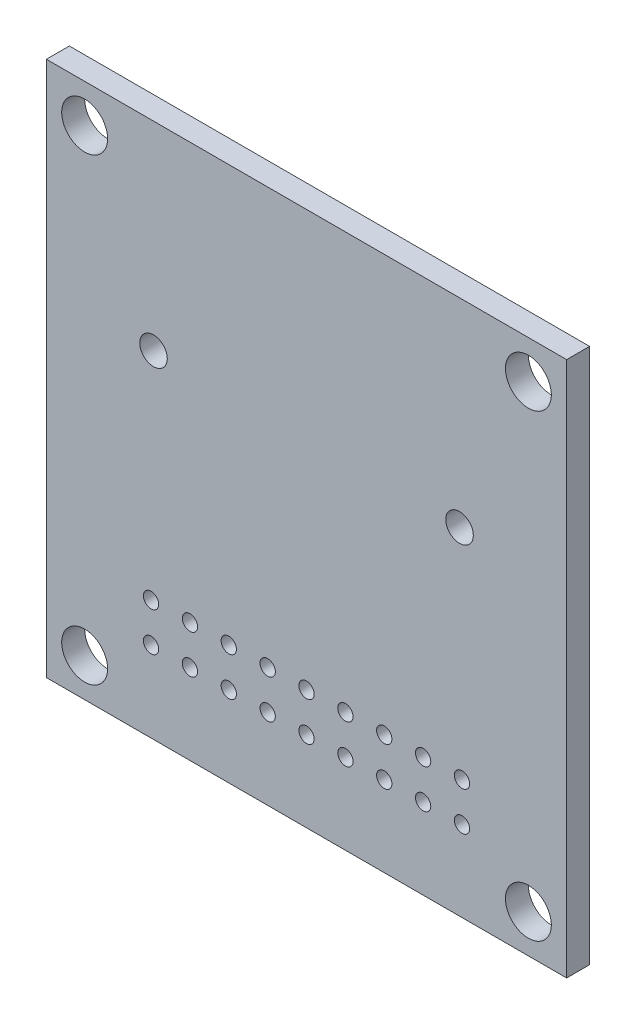
SolidWorks part; units mm, degrees
ref_plane "Front Plane" through (0, 0, 0) normal (0, 0, 1) x (1, 0, 0)
ref_plane "Top Plane" through (0, 0, 0) normal (0, 1, 0) x (1, 0, 0)
ref_plane "Right Plane" through (0, 0, 0) normal (1, 0, 0) x (0, 0, -1)
sketch "Sketch1" plane through (0, 0, 0) normal (0, 0, 1) x (1, 0, 0)
  line L0 (0, 0) -> (0, 8.3377) construction
  line L1 (17, -17.5) -> (-17, -17.5)
  line L2 (17, -17.5) -> (17, 17.5)
  line L3 (17, 17.5) -> (-17, 17.5)
  line L4 (-17, -17.5) -> (-17, 17.5)
  line L5 (17, -17.5) -> (-17, 17.5) construction
  line L6 (17, 17.5) -> (-17, -17.5) construction
  line L7 (0, 0) -> (4.1078, 0) construction
  circle A0 centre (-14.5, 15) radius 1.5
  circle A1 centre (-14.5, -15) radius 1.5
  circle A2 centre (14.5, -15) radius 1.5
  circle A3 centre (14.5, 15) radius 1.5
  point P0 (0, 0)
  dimension "D3" = 3
  dimension "D4" = 29
  dimension "D1" = 34
  dimension "D2" = 35
  dimension "D5" = 30
extrude "Board" add sketch "Sketch1" along normal blind 1.5
sketch "Sketch2" plane through (0, 0, 0) normal (0, 0, -1) x (-1, 0, 0)
  line L0 (17, -17.5) -> (-17, -17.5) construction
  circle A0 centre (-10, 4.5) radius 0.9
  circle A1 centre (10, 4.5) radius 0.9
  circle A2 centre (10.16, -9.69) radius 0.5
  circle A3 centre (10.16, -12.23) radius 0.5
  circle A4 centre (7.62, -12.23) radius 0.5
  circle A5 centre (7.62, -9.69) radius 0.5
  circle A6 centre (5.08, -12.23) radius 0.5
  circle A7 centre (5.08, -9.69) radius 0.5
  circle A8 centre (2.54, -12.23) radius 0.5
  circle A9 centre (2.54, -9.69) radius 0.5
  circle A10 centre (0, -12.23) radius 0.5
  circle A11 centre (0, -9.69) radius 0.5
  circle A12 centre (-2.54, -12.23) radius 0.5
  circle A13 centre (-2.54, -9.69) radius 0.5
  circle A14 centre (-5.08, -12.23) radius 0.5
  circle A15 centre (-5.08, -9.69) radius 0.5
  circle A16 centre (-7.62, -12.23) radius 0.5
  circle A17 centre (-7.62, -9.69) radius 0.5
  circle A18 centre (-10.16, -12.23) radius 0.5
  circle A19 centre (-10.16, -9.69) radius 0.5
  dimension "D1" = 1.8
  dimension "D7" = 1
  dimension "D2" = 20
  dimension "D3" = 4.5
  dimension "D4" = 10
  dimension "D5" = 2.54
  dimension "D6" = 5.27
  dimension "D9" = 10.16
  dimension "D8" = 9
extrude "Holes" cut sketch "Sketch2" against normal blind 2
